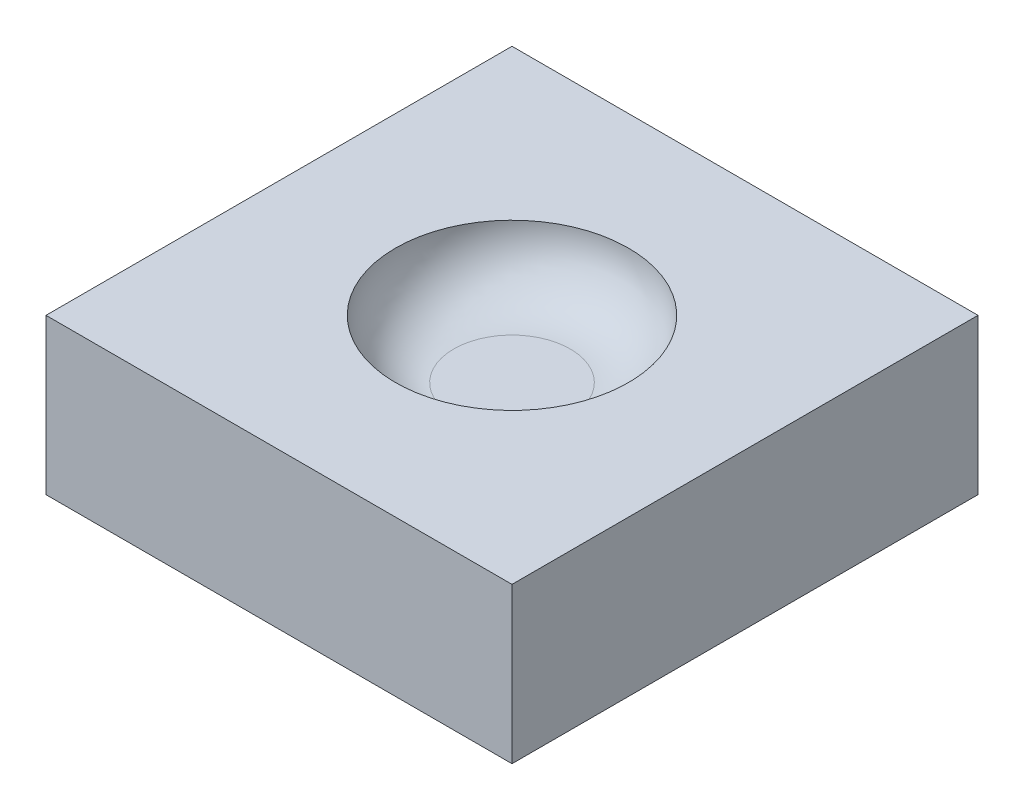
SolidWorks part; units mm, degrees
ref_plane "Front Plane" through (0, 0, 0) normal (0, 0, 1) x (1, 0, 0)
ref_plane "Top Plane" through (0, 0, 0) normal (0, 1, 0) x (1, 0, 0)
ref_plane "Right Plane" through (0, 0, 0) normal (1, 0, 0) x (0, 0, -1)
sketch "Sketch2" plane through (0, 0, 0) normal (0, 1, 0) x (1, 0, 0)
  line L1 (-76.2, -76.2) -> (76.2, -76.2)
  line L2 (-76.2, -76.2) -> (-76.2, 76.2)
  line L3 (-76.2, 76.2) -> (76.2, 76.2)
  line L4 (76.2, -76.2) -> (76.2, 76.2)
  point P0 (0, 76.2)
  point P6 (0, 0)
  point P7 (0, 0)
  point P9 (-76.2, 0)
  dimension "D1" = 152.4
  dimension "D2" = 152.4
extrude "Boss-Extrude1" add sketch "Sketch2" along normal blind 50.8
sketch "Sketch3" plane through (0, 0, 0) normal (0, 0, 1) x (1, 0, 0)
  line L0 (-19.05, 50.8) -> (0, 50.8) construction
  line L1 (-76.2, 50.8) -> (76.2, 50.8) construction
  line L3 (-19.05, 31.75) -> (0, 31.75)
  line L4 (-38.1, 50.8) -> (0, 50.8)
  line L6 (0, 50.8) -> (0, 31.75)
  line L8 (0, 50.8) -> (-38.1, 50.8)
  arc A0 (-38.1, 50.8) -> (-19.05, 31.75) centre (-19.05, 50.8) ccw
  point P4 (0, 50.8)
  point P5 (0, 0)
  point P6 (0, 0)
  point P8 (0, 0)
  point P12 (0, 0)
  point P14 (-18.0069, 101.6)
  point P15 (-8.1676, 101.6)
  point P16 (-12.4375, 82.55)
  point P17 (0, 0)
  point P18 (0, 0)
  dimension "D1" = 38.1
  dimension "D3" = 19.05
  dimension "D2" = 19.05
revolve "Cut-Revolve1" cut sketch "Sketch3" angle 360 about L6
